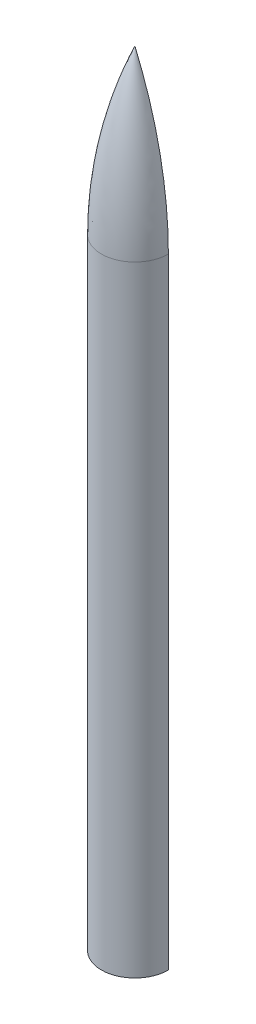
SolidWorks part; units mm, degrees
material "Custom Plastic"
ref_plane "Front Plane" through (0, 0, 0) normal (0, 0, 1) x (1, 0, 0)
ref_plane "Top Plane" through (0, 0, 0) normal (0, 1, 0) x (1, 0, 0)
ref_plane "Right Plane" through (0, 0, 0) normal (1, 0, 0) x (0, 0, -1)
sketch "Sketch3" plane through (0, 0, 0) normal (0, 0, 1) x (1, 0, 0)
  line L0 (0, 0) -> (0, 3209.544) construction
  line L1 (0, 0) -> (-137.16, 0) construction
  line L2 (-137.16, 0) -> (-137.16, 2540)
  line L3 (-133.985, 0) -> (-133.985, 2540)
  line L4 (0, 3209.544) -> (0, 3201.4278)
  line L5 (-137.16, 0) -> (-133.985, 0)
  arc A0 (-137.16, 2540) -> (0, 3209.544) centre (1565.6033, 2540) cw
  arc A1 (-133.985, 2540) -> (0, 3201.4278) centre (1565.6033, 2540) cw
  arc A2 (-133.985, 2540) -> (2.9192, 3208.2956) centre (1565.6033, 2540) cw construction
  dimension "D1" = 3209.544
  dimension "D2" = 137.16
  dimension "D3" = 2540
  dimension "D4" = 3.175
revolve "Revolve1" add sketch "Sketch3" angle 180 about L0
